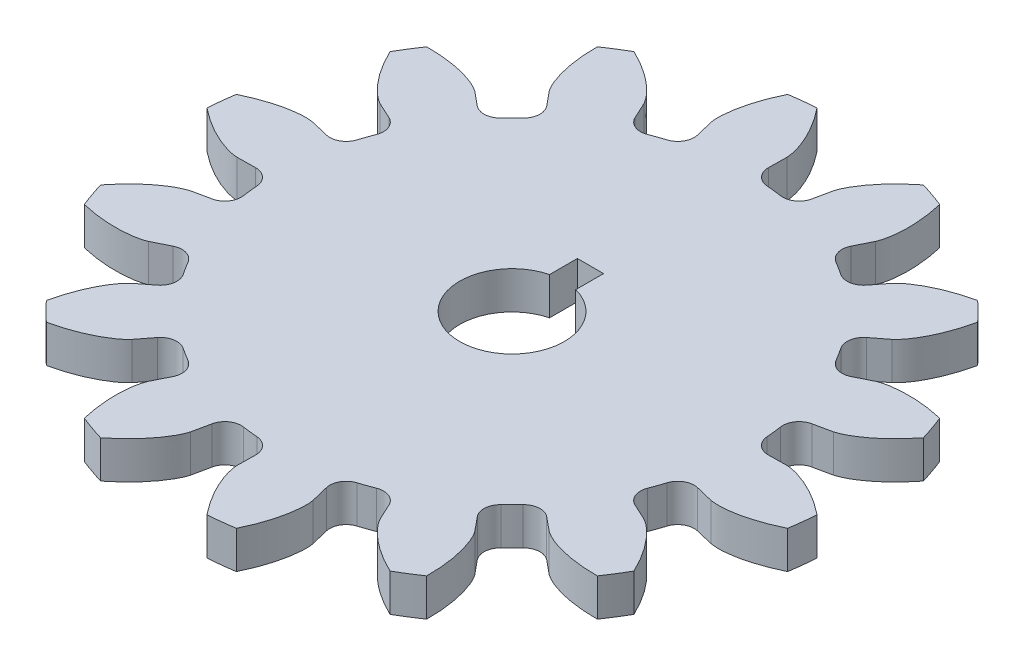
SolidWorks part; units mm, degrees
ref_plane "Front Plane" through (0, 0, 0) normal (0, 0, 1) x (1, 0, 0)
ref_plane "Top Plane" through (0, 0, 0) normal (0, 1, 0) x (1, 0, 0)
ref_plane "Right Plane" through (0, 0, 0) normal (1, 0, 0) x (0, 0, -1)
sketch "Sketch3" plane through (0, 0, 0) normal (0, 1, 0) x (1, 0, 0)
  line L0 (0, 0) -> (0, 60.2244) construction
  line L1 (-46.7317, 35) -> (46.7317, 35) construction
  line L2 (0, 35) -> (42.6743, 50.5322) construction
  line L3 (0, 35) -> (-37.272, 21.4341) construction
  line L4 (0, 0) -> (-11.2488, 30.9058) construction
  line L5 (0, 0) -> (-15.7994, 28.8458) construction
  line L6 (-15.7994, 28.8458) -> (-0.9151, 36.9982) construction
  line L7 (0, 0) -> (-19.9856, 26.1204) construction
  line L8 (-19.9856, 26.1204) -> (-2.5366, 39.4713) construction
  line L9 (0, 0) -> (-6.4387, 32.2528) construction
  line L10 (-6.4387, 32.2528) -> (0.3972, 33.6175) construction
  line L11 (0, 0) -> (-23.7108, 22.7925) construction
  line L12 (-23.7108, 22.7925) -> (-5.0199, 42.2365) construction
  circle A0 centre (0, 0) radius 35 construction
  circle A2 centre (0, 0) radius 32.8892 construction
  arc A3 (-11.2488, 30.9058) -> (-15.7994, 28.8458) centre (0, 0) ccw
  arc A4 (-11.2488, 30.9058) -> (-19.9856, 26.1204) centre (0, 0) ccw
  arc A5 (-11.2488, 30.9058) -> (-6.4387, 32.2528) centre (0, 0) cw
  arc A6 (-11.2488, 30.9058) -> (0.4902, 32.8856) centre (0, 0) cw
  arc A7 (-11.2488, 30.9058) -> (-23.7108, 22.7925) centre (0, 0) ccw
  point P7 (0, 35)
  point P10 (0, 35)
  dimension "D1" = 70
  dimension "D2" = 20
  dimension "D3" = 11.9707
  dimension "D5" = 16.9707
  dimension "D7" = 21.9707
  dimension "D9" = 6.9707
  dimension "D12" = 26.9707
  dimension "D4" = 5
  dimension "D6" = 10
  dimension "D8" = 5
  dimension "D10" = 11.9707
  dimension "D11" = 15
sketch "Sketch4" plane through (0, 0, 0) normal (0, 1, 0) x (1, 0, 0)
  line L0 (-3.219, 28.5692) -> (-4.4786, 39.7485) construction
  line L1 (0, 0) -> (0, 60.2244) construction
  line L2 (0.4902, 32.8856) -> (0.4285, 28.7468)
  line L3 (-6.8145, 27.9307) -> (-7.7956, 31.952)
  arc A0 (-2.8716, 39.8968) -> (-6.0783, 39.5355) centre (0, 0) ccw
  arc A1 (0.4285, 28.7468) -> (-6.8145, 27.9307) centre (0, 0) ccw
  spline S2 degree 3 poles (-2.8716, 39.8968) (-2.7582, 39.7563) (-2.0352, 38.8382) (-0.9811, 37.2512) (0.0536, 35.0296) (0.4465, 33.6128) (0.4902, 32.8856) knots 0.287498 0.287498 0.287498 0.287498 0.33641 0.604083 0.803019 1 1 1 1
  spline S3 degree 3 poles (-6.0783, 39.5355) (-6.1575, 39.3733) (-6.6581, 38.3173) (-7.3326, 36.5356) (-7.8471, 34.1394) (-7.9148, 32.6707) (-7.7956, 31.952) knots 0.287498 0.287498 0.287498 0.287498 0.33641 0.604083 0.803019 1 1 1 1
  dimension "D1" = 6.429
sketch "Sketch5" plane through (0, 0, 0) normal (0, 1, 0) x (1, 0, 0)
  circle A0 centre (0, 0) radius 28.75
extrude "Boss-Extrude1" add sketch "Sketch5" along normal up to surface (4.5542 mm away)
extrude "Boss-Extrude2" add sketch "Sketch4" along normal up to surface (4.5542 mm away) up to face at (0, 4.5542, -28.75)
fillet "Fillet1" radius 2 2 edges at (-6.8145, 2.2771, -27.9307) (0.4285, 2.2771, -28.7468)
pattern_circular "CirPattern1" count 14 over 360 about axis through (0, 85.8715, 0) along (0, -1, 0) of "Boss-Extrude2", "Fillet1"
sketch "Sketch6" plane through (0, 0, 0) normal (0, 1, 0) x (1, 0, 0)
  line L2 (-1.5875, 9.525) -> (1.5875, 9.525)
  line L6 (1.5875, 6.1484) -> (1.5875, 9.525)
  line L8 (-1.5875, 6.1484) -> (-1.5875, 9.525)
  arc A0 (-1.5875, 6.1484) -> (1.5875, 6.1484) centre (0, 0) ccw
extrude "Cut-Extrude3" cut sketch "Sketch6" along normal up to surface (4.5542 mm away) up to face at (0, 4.5542, 0)
sketch "Sketch7" plane through (0, 4.5542, 0) normal (0, 1, 0) x (1, 0, 0)
  circle A0 centre (0, 0) radius 35
sketch "Sketch8" plane through (0, 4.5542, 0) normal (0, 1, 0) x (1, 0, 0)
  circle A0 centre (0, 0) radius 36
equation "\"D5@Sketch3\"=\"D3@Sketch3\"+\"D4@Sketch3\""
equation "\"D7@Sketch3\"=\"D3@Sketch3\"+\"D6@Sketch3\""
equation "\"D9@Sketch3\"=\"D3@Sketch3\"-\"D8@Sketch3\""
equation "\"D10@Sketch3\"=\"D3@Sketch3\""
equation "\"D1@Sketch4\"=360/14/4"
equation "\"D12@Sketch3\"=\"D3@Sketch3\"+\"D11@Sketch3\""
